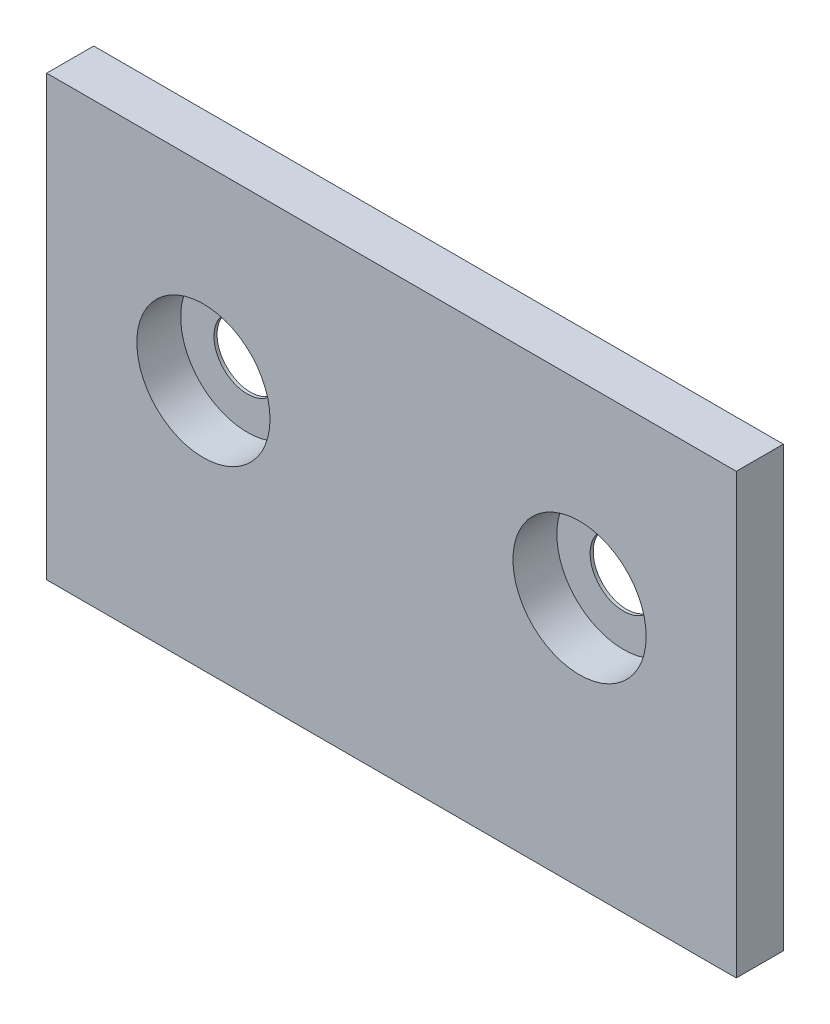
SolidWorks part; units mm, degrees
material "Brass"
ref_plane "Front Plane" through (0, 0, 0) normal (0, 0, 1) x (1, 0, 0)
ref_plane "Top Plane" through (0, 0, 0) normal (0, 1, 0) x (1, 0, 0)
ref_plane "Right Plane" through (0, 0, 0) normal (1, 0, 0) x (0, 0, -1)
sketch "Sketch1" plane through (0, 0, 0) normal (0, 0, 1) x (1, 0, 0)
  line L8 (12.7, 42.8625) -> (12.7, 39.6875)
  line L9 (12.7, 39.6875) -> (34.925, 39.6875)
  line L10 (34.925, 39.6875) -> (34.925, 84.1375)
  line L11 (34.925, 84.1375) -> (-34.925, 84.1375)
  line L12 (-34.925, 84.1375) -> (-34.925, 39.6875)
  line L13 (-34.925, 39.6875) -> (-12.7, 39.6875)
  line L14 (-12.7, 39.6875) -> (-12.7, 42.8625)
  line L15 (-12.7, 42.8625) -> (12.7, 42.8625)
  line L17 (-34.925, 39.6875) -> (34.925, 39.6875)
  line L18 (34.925, 39.6875) -> (34.925, 84.1375)
  line L19 (34.925, 84.1375) -> (-34.925, 84.1375)
  line L20 (-34.925, 84.1375) -> (-34.925, 39.6875)
  dimension "D1" = 0
extrude "Extrude1" add sketch "Sketch1" along normal blind 4.7625
hole_wizard "CBORE for 1/4 Pan Head Machine Screw1" positions "Sketch5" profile "Sketch4" counterbore size "1/4" standard "Ansi Inch" end condition through all
sketch "Sketch5" plane through (0, 0, 4.7625) normal (0, 0, 1) x (1, 0, 0)
  line L0 (-34.925, 39.6875) -> (34.925, 39.6875) construction
  point P0 (-19.05, 65.0875)
  point P1 (19.05, 65.0875)
  dimension "D1" = 38.1
  dimension "D2" = 25.4
sketch "Sketch4" plane through (-19.05, 65.0875, 4.7625) normal (1, 0, 0) x (0, -1, 0)
  line L0 (0, 0) -> (0, 4.7625)
  line L1 (0, 4.7625) -> (3.3782, 4.7625)
  line L3 (3.3782, 4.7625) -> (3.3782, 4.445)
  line L4 (3.3782, 4.445) -> (6.7462, 4.445)
  line L5 (6.7462, 4.445) -> (6.7462, 0)
  line L7 (6.7462, 0) -> (0, 0)
  line L11 (0, -6.35) -> (0, 107.95) construction
  dimension "Thru Hole Dia." = 6.7564
  dimension "Thru Hole Depth" = 4.7625
  dimension "C'Bore Dia." = 13.4925
  dimension "C'Bore Depth" = 4.445
